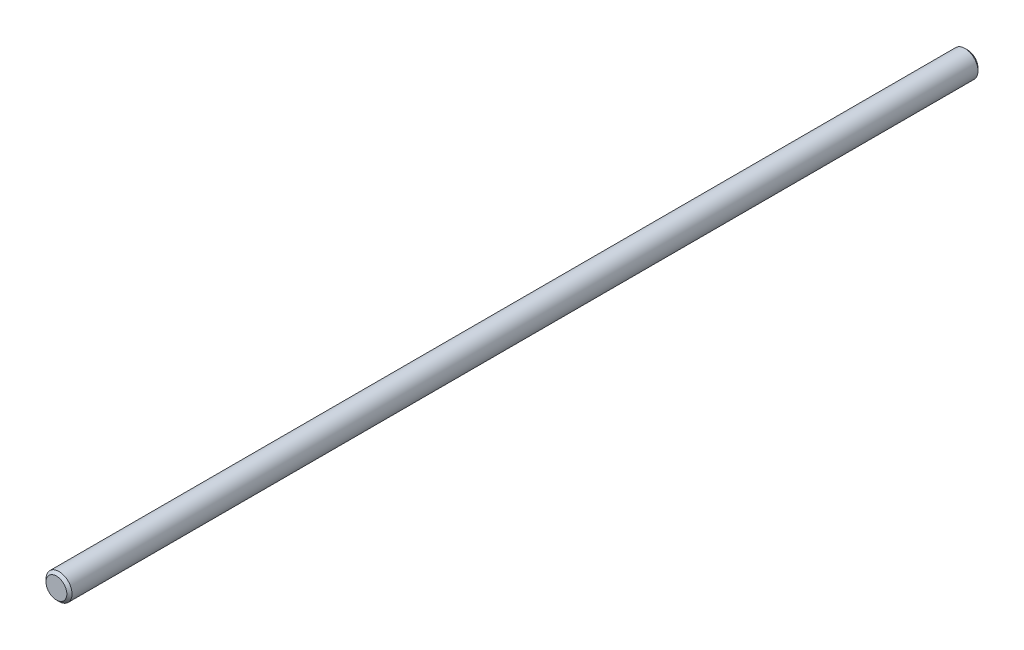
SolidWorks part; units mm, degrees
ref_plane "Front Plane" through (0, 0, 0) normal (0, 0, 1) x (1, 0, 0)
ref_plane "Top Plane" through (0, 0, 0) normal (0, 1, 0) x (1, 0, 0)
ref_plane "Right Plane" through (0, 0, 0) normal (1, 0, 0) x (0, 0, -1)
sketch "Sketch1" plane through (0, 0, 0) normal (0, 0, 1) x (1, 0, 0)
  circle A0 centre (0, 0) radius 2.5
  dimension "D1" = 5
extrude "Extrude1" add sketch "Sketch1" along normal blind 175
chamfer "Chamfer1" distance 0.5 angle 45 2 edges at (2.5, 0, 0) (2.5, 0, 175)
